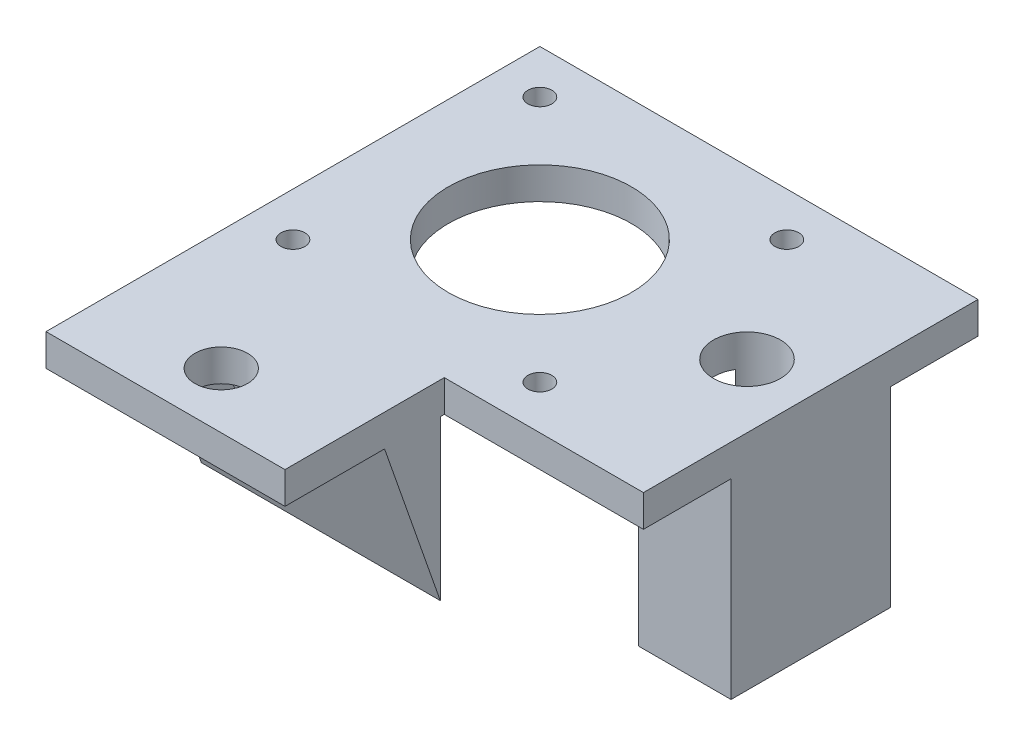
SolidWorks part; units mm, degrees
ref_plane "Front Plane" through (0, 0, 0) normal (0, 0, 1) x (1, 0, 0)
ref_plane "Top Plane" through (0, 0, 0) normal (0, 1, 0) x (1, 0, 0)
ref_plane "Right Plane" through (0, 0, 0) normal (1, 0, 0) x (0, 0, -1)
sketch "Sketch1" plane through (0, 0, 0) normal (0, 1, 0) x (1, 0, 0)
  line L0 (0, 21) -> (55, 21) construction
  line L2 (0, 0) -> (0, 42)
  line L3 (0, 42) -> (55, 42)
  line L4 (55, 0) -> (55, 42)
  line L5 (21, 42) -> (21, 0) construction
  line L6 (0, 0) -> (0, -20)
  line L7 (0, -20) -> (30, -20)
  line L8 (30, -20) -> (30, 0)
  line L9 (15, -20) -> (15, 0) construction
  line L13 (30, 0) -> (55, 0)
  line L14 (30, 0) -> (0, 0) construction
  circle A0 centre (47, 21) radius 4.2
  circle A1 centre (21, 21) radius 11.5
  circle A2 centre (5.5, 36.5) radius 1.5
  circle A3 centre (36.5, 36.5) radius 1.5
  circle A4 centre (5.5, 5.5) radius 1.5
  circle A5 centre (36.5, 5.5) radius 1.5
  circle A6 centre (15, -13) radius 3.3
  point P8 (55, 21)
  dimension "D2" = 23
  dimension "D4" = 8.4
  dimension "D9" = 3
  dimension "D13" = 6.6
  dimension "D1" = 26
  dimension "D3" = 42
  dimension "D5" = 21
  dimension "D6" = 55
  dimension "D7" = 15.5
  dimension "D8" = 15.5
  dimension "D10" = 30
  dimension "D11" = 20
  dimension "D12" = 13
extrude "Boss-Extrude1" add sketch "Sketch1" along normal blind 4
sketch "Sketch2" plane through (0, 0, 0) normal (0, -1, 0) x (1, 0, 0)
  line L1 (40.4, 0) -> (43.4, 0)
  line L2 (40.4, 0) -> (40.4, -42)
  line L3 (40.4, -42) -> (43.4, -42)
  line L4 (43.4, 0) -> (43.4, -42)
  line L5 (55, -42) -> (0, -42) construction
  line L6 (55, 0) -> (55, -42) construction
  line L7 (55, -11) -> (43.4, -11)
  line L8 (55, -11) -> (55, -31)
  line L9 (55, -31) -> (43.4, -31)
  line L10 (43.4, -11) -> (43.4, -31)
  line L11 (30, 0) -> (55, 0) construction
  circle A0 centre (47, -21) radius 6.6
  circle A1 centre (47, -21) radius 4.2
  circle A2 centre (47, -21) radius 4.2 construction
  point P25 (55, -21)
  point P26 (55, -21)
  circle M7 centre (47, -21) radius 4.2
  line M10 (55, -42) -> (55, 0)
  dimension "D1" = 2.4
  dimension "D2" = 3
  dimension "D3" = 20
extrude "Boss-Extrude2" add sketch "Sketch2" along normal blind 20 contours L4 A0 L10 M7 | A0 L10 L9 L7 L4 M10
sketch "Sketch3" plane through (0, -20, 0) normal (0, -1, 0) x (1, 0, 0)
  line L1 (55, -31) -> (43.4, -31)
  line L2 (55, -31) -> (55, -11)
  line L3 (55, -11) -> (43.4, -11)
  line L4 (43.4, -31) -> (43.4, -11)
extrude "Boss-Extrude3" add sketch "Sketch3" along normal blind 4
sketch "Sketch4" plane through (0, 0, 0) normal (-1, 0, 0) x (0, 0, 1)
  line L0 (-42, 0) -> (0.5, 0) construction
  line L1 (-42, 0) -> (20, 0) construction
  line L2 (0.5, 0) -> (7.5, 0)
  line L3 (7.5, 0) -> (0.5, -20)
  line L4 (0.5, -20) -> (0.5, 0)
  dimension "D1" = 42.5
  dimension "D2" = 7
  dimension "D3" = 20
extrude "Boss-Extrude4" add sketch "Sketch4" against normal up to surface (30 mm away) up to face at (30, 2, 10)
sketch "Sketch5" plane through (0, 0, 0) normal (0, -1, 0) x (1, 0, 0)
  circle A0 centre (15, 13) radius 8.75
  dimension "D1" = 17.5
extrude "Cut-Extrude1" cut sketch "Sketch5" along normal through all
equation "\"8mm hole\" = 8.4mm"
equation "\"22mm hole\"= 23mm"
equation "\"D2@Sketch1\"=\"22mm hole\""
equation "\"D4@Sketch1\"=\"8mm hole\""
equation "\"15mm hole\"= 15.8mm"
equation "\"D1@Sketch3\"= \"8mm hole\""
equation "\"bed height offset\"= 3mm"
equation "\"motor width\"= 42.5mm"
equation "\"D1@Sketch4\"= \"motor width\""
